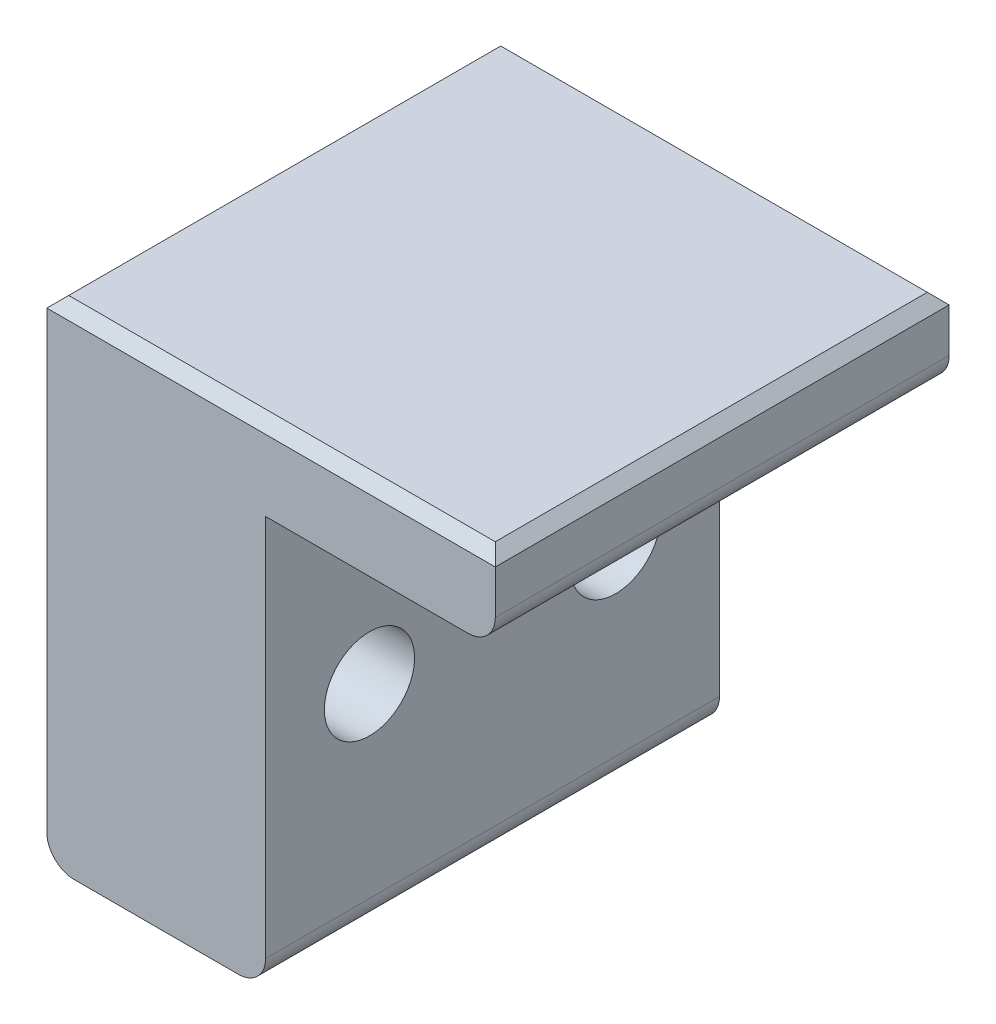
SolidWorks part; units mm, degrees
ref_plane "Front Plane" through (0, 0, 0) normal (0, 0, 1) x (1, 0, 0)
ref_plane "Top Plane" through (0, 0, 0) normal (0, 1, 0) x (1, 0, 0)
ref_plane "Right Plane" through (0, 0, 0) normal (1, 0, 0) x (0, 0, -1)
sketch "Sketch1" plane through (0, 0, 0) normal (0, 0, 1) x (1, 0, 0)
  line L0 (0, 0) -> (8.4, 0)
  line L1 (8.4, 0) -> (8.4, 3)
  line L2 (8.4, 3) -> (-8, 3)
  line L3 (-8, 3) -> (-8, -15)
  line L4 (-8, -15) -> (0, -15)
  line L5 (0, -15) -> (0, 0)
  dimension "D1" = 3
  dimension "D2" = 16.4
  dimension "D3" = 8
  dimension "D4" = 18
extrude "Boss-Extrude1" add sketch "Sketch1" along normal blind 16.6
sketch "Sketch2" plane through (-8, 0, 0) normal (-1, 0, 0) x (0, 0, 1)
  line L0 (3.8, -7.2) -> (12.8, -7.2) construction
  line L1 (16.6, 3) -> (0, 3) construction
  line L2 (16.6, 3) -> (0, 3) construction
  circle A2 centre (3.8, -7.2) radius 1.65
  circle A3 centre (12.8, -7.2) radius 1.65
  point P6 (8.3, 3)
  point P7 (8.3, -7.2)
  dimension "D2" = 3.3
  dimension "D1" = 10.2
  dimension "D3" = 9
extrude "Cut-Extrude1" cut sketch "Sketch2" against normal through all
chamfer "Chamfer1" distance 0.4 angle 45 4 edges at (8.4, 3, 8.3) (0.2, 3, 16.6) (-8, 3, 8.3) (0.2, 3, 0)
fillet "Fillet1" radius 1 3 edges at (-8, -15, 8.3) (0, -15, 8.3) (8.4, 0, 8.3)
